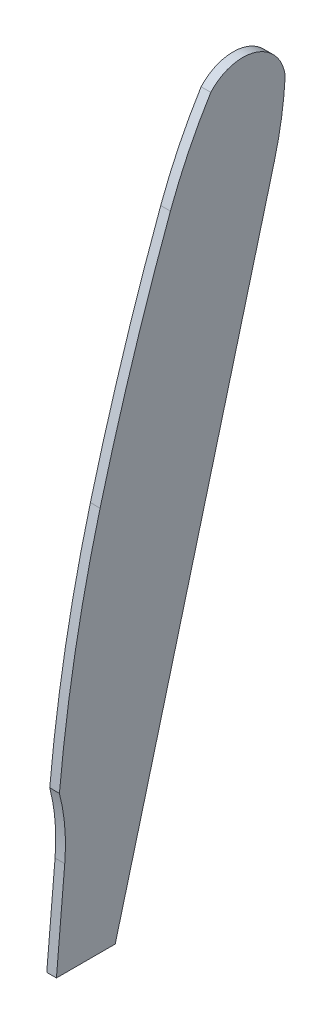
SolidWorks part; units mm, degrees
ref_plane "Front Plane" through (0, 0, 0) normal (0, 0, 1) x (1, 0, 0)
ref_plane "Top Plane" through (0, 0, 0) normal (0, 1, 0) x (1, 0, 0)
ref_plane "Right Plane" through (0, 0, 0) normal (1, 0, 0) x (0, 0, -1)
sketch "Sketch1" plane through (0, 0, 0) normal (1, 0, 0) x (0, 0, -1)
  line L0 (2.2636, 3.4083) -> (1191.597, 3.4083) construction
  line L1 (-71.2618, -25.3172) -> (-91.7785, -25.3172)
  line L2 (-91.7785, -25.3172) -> (-159.1308, -411.4808)
  line L3 (-71.2618, -25.3172) -> (-54.5618, -25.3172)
  line L4 (-54.5618, -25.3172) -> (-54.5618, -82.4405)
  line L5 (-47.6773, -122.2812) -> (-47.6773, -276.2133)
  line L6 (-47.6773, -276.2133) -> (-76.1168, -411.4808)
  arc A0 (-159.1308, -411.4808) -> (-164.8692, -458.2855) centre (299.3506, -491.4463) ccw
  arc A1 (-164.8692, -458.2855) -> (-161.595, -467.7693) centre (-152.1323, -459.1953) ccw
  arc A2 (-161.595, -467.7693) -> (-116.2081, -467.7693) centre (-138.9015, -447.2072) ccw
  arc A3 (-54.5618, -82.4405) -> (-47.6773, -122.2812) centre (64.1606, -82.4405) ccw
  arc A4 (-76.1168, -411.4808) -> (-116.2081, -467.7693) centre (-160.6223, -393.7138) cw
sketch "Sketch2" plane through (0, 0, 0) normal (1, 0, 0) x (0, 0, -1)
  line L1 (37.3589, 0) -> (138.1112, 378.8239)
  line L3 (0, 0) -> (5.2624, 60.1495)
  line L6 (37.3589, 0) -> (0, 0)
  line L7 (0, 0) -> (311.5505, 0) construction
  line L8 (98.563, 438.7875) -> (5.2624, 60.1495) construction
  line L9 (130.0367, 445.2441) -> (18.6794, 0) construction
  line L10 (29.6587, 101.5508) -> (4.2604, 0) construction
  line L11 (0, 0) -> (71.0581, 0) construction
  line L12 (22.4802, 100.0782) -> (1.2002, 13.7188) construction
  line L13 (8.5208, 0) -> (31.5003, 86.4018)
  line L14 (0, 0) -> (1.2002, 13.7188)
  line L15 (8.5208, 0) -> (0, 0)
  arc A0 (138.1112, 378.8239) -> (147.9071, 424.9504) centre (-311.656, 498.4444) ccw
  arc A1 (147.9071, 424.9504) -> (145.472, 434.6835) centre (135.298, 426.9669) ccw
  arc A2 (145.472, 434.6835) -> (111.3524, 444.4271) centre (121.9195, 416.8197) ccw
  arc A3 (5.2624, 60.1495) -> (1.8765, 100.4386) centre (-113.0082, 70.4969) ccw
  arc A4 (55.07, 384.8996) -> (111.3524, 444.4271) centre (140.8841, 360.1345) cw
  arc A5 (14.4489, 244.1423) -> (1.8765, 100.4386) centre (374.476, 140.2422) ccw
  arc A6 (14.4489, 244.1423) -> (55.07, 384.8996) centre (1537.6812, -119.2067) cw
  arc A7 (3.2955, 55.6837) -> (12.5603, 87.7875) centre (350.7128, -27.1886) cw
  arc A8 (31.5003, 86.4018) -> (33.7345, 96.9223) centre (-71.0822, 113.6847) ccw
  arc A9 (12.5603, 87.7875) -> (25.3971, 101.3645) centre (32.1327, 82.1391) cw
  arc A10 (33.1791, 99.1422) -> (25.3971, 101.3645) centre (27.8073, 95.0678) ccw
  arc A11 (3.2955, 55.6837) -> (0.428, 22.9079) centre (85.4101, 31.9863) ccw
  arc A12 (33.7345, 96.9223) -> (33.1791, 99.1422) centre (30.8586, 97.3822) ccw
  arc A13 (1.2002, 13.7188) -> (0.428, 22.9079) centre (-25.7748, 16.0789) ccw
  dimension "D1" = 85
  dimension "D2" = 445.2441
sketch "Sketch5" plane through (0, 0, 0) normal (1, 0, 0) x (0, 0, -1)
  line L2 (28.7382, 101.55) -> (4.25, 0) construction
  line L3 (-0.0104, 0) -> (71.0472, 0) construction
  line L5 (8.5, 0) -> (31.4962, 86.4645)
  line L6 (0, 0) -> (1.2002, 13.7187)
  line L7 (8.5, 0) -> (0, 0)
  arc A0 (16.4793, 87.7992) -> (22.3212, 99.7571) centre (78.6382, 64.8382) cw
  arc A1 (6.3096, 55.6833) -> (16.4793, 87.7992) centre (351.5139, -35.96) cw
  arc A2 (31.4962, 86.4645) -> (33.0874, 96.5026) centre (-16.3926, 99.2011) ccw
  arc A4 (33.0874, 96.5026) -> (22.3212, 99.7571) centre (26.9406, 95.6036) ccw
  arc A7 (1.2002, 13.7187) -> (0.428, 22.9078) centre (-25.7746, 16.0787) ccw
  arc A8 (6.3096, 55.6833) -> (0.428, 22.9078) centre (202.9443, 3.4816) ccw
  point P0 (23.3096, 55.6833)
  dimension "D3" = 85
  dimension "D1" = 101.55
  dimension "D2" = 8.5
extrude "Boss-Extrude1" add sketch "Sketch5" along normal blind 1.4
